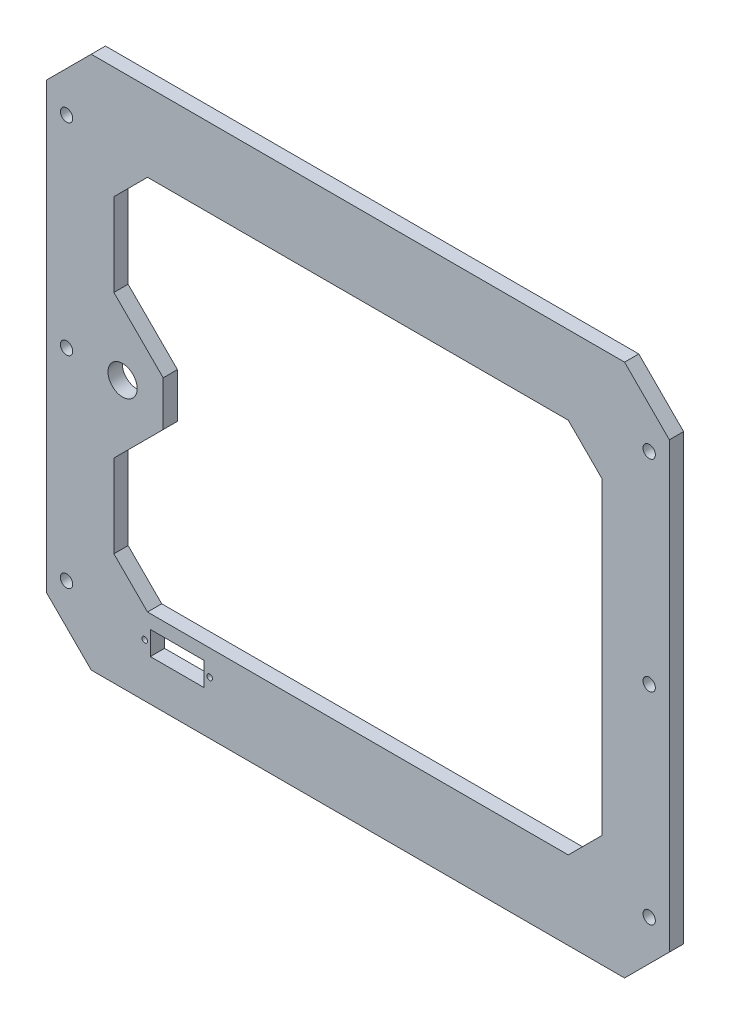
SolidWorks part; units mm, degrees
ref_plane "Front Plane" through (0, 0, 0) normal (0, 0, 1) x (1, 0, 0)
ref_plane "Top Plane" through (0, 0, 0) normal (0, 1, 0) x (1, 0, 0)
ref_plane "Right Plane" through (0, 0, 0) normal (1, 0, 0) x (0, 0, -1)
sketch "Sketch1" plane through (0, 0, 0) normal (0, 0, 1) x (1, 0, 0)
  line L0 (-79.0045, 0) -> (94.053, 0) construction
  line L1 (0, 67.0127) -> (0, -68.6587) construction
  line L3 (139, -119) -> (-139, -119)
  line L4 (139, -119) -> (139, 119)
  line L5 (139, 119) -> (-139, 119)
  line L6 (-139, -119) -> (-139, 119)
  line L7 (139, -119) -> (-139, 119) construction
  line L8 (139, 119) -> (-139, -119) construction
  point P4 (0, 0)
  dimension "D1" = 238
  dimension "D2" = 278
extrude "Boss-Extrude1" add sketch "Sketch1" along normal blind 6.35
chamfer "Chamfer1" distance 20 angle 45 4 edges at (139, -119, 3.175) (139, 119, 3.175) (-139, 119, 3.175) (-139, -119, 3.175)
sketch "Sketch4" plane through (0, 0, 6.35) normal (0, 0, 1) x (1, 0, 0)
  line L0 (0, 186.846) -> (0, -174.5938) construction
  line L1 (219.7737, 0) -> (-232.7917, 0) construction
  line L4 (-139, 99) -> (-139, -99) construction
  circle A6 centre (-130, 90) radius 2.75
  circle A7 centre (-130, -90) radius 2.75
  circle A8 centre (-130, 0) radius 2.75
  circle A9 centre (130, -90) radius 2.75
  circle A10 centre (130, 0) radius 2.75
  circle A11 centre (130, 90) radius 2.75
  dimension "D6" = 5.5
  dimension "D7" = 5.5
  dimension "D4" = 9
  dimension "D5" = 90
extrude "Cut-Extrude2" cut sketch "Sketch4" against normal blind 76.2
sketch "Sketch5" plane through (0, 0, 6.35) normal (0, 0, 1) x (1, 0, 0)
  line L0 (-139, 99) -> (-139, -99) construction
  line L1 (119, 119) -> (-119, 119) construction
  line L2 (93.8757, -84) -> (-93.8757, -84)
  line L3 (108.8757, -69) -> (108.8757, 69)
  line L4 (93.8757, 84) -> (-93.8757, 84)
  line L5 (-108.8757, -69) -> (-108.8757, -32)
  line L6 (108.8757, -84) -> (-108.8757, 84) construction
  line L7 (108.8757, 84) -> (-108.8757, -84) construction
  line L8 (-108.8757, 69) -> (-93.8757, 84)
  line L9 (108.8757, 69) -> (93.8757, 84)
  line L10 (93.8757, -84) -> (108.8757, -69)
  line L11 (-93.8757, -84) -> (-108.8757, -69)
  line L12 (-109, 0) -> (0, 0) construction
  line L13 (-108.8757, 32) -> (-86.8757, 10)
  line L14 (-86.8757, 10) -> (-86.8757, -10)
  line L15 (-108.8757, -32) -> (-86.8757, -10)
  line L16 (-108.8757, 32) -> (-108.8757, 69)
  circle A0 centre (-105, 0) radius 6.5
  point P4 (0, 0)
  point P26 (-86.8757, 0)
  point P27 (0, 0)
  dimension "D1" = 13
  dimension "D2" = 34
  dimension "D3" = 35
  dimension "D4" = 45
  dimension "D5" = 20
  dimension "D10" = 22
extrude "Cut-Extrude3" cut sketch "Sketch5" against normal blind 10
sketch "Sketch7" plane through (0, 0, 6.35) normal (0, 0, 1) x (1, 0, 0)
  line L0 (-80.6158, -78.493) -> (-80.6158, -110.3099) construction
  line L1 (-92.6158, -90.0921) -> (-68.6158, -90.0921)
  line L2 (-92.6158, -90.0921) -> (-92.6158, -100.5921)
  line L3 (-92.6158, -100.5921) -> (-68.6158, -100.5921)
  line L4 (-68.6158, -90.0921) -> (-68.6158, -100.5921)
  line L5 (-92.6158, -90.0921) -> (-68.6158, -100.5921) construction
  line L6 (-92.6158, -100.5921) -> (-68.6158, -90.0921) construction
  circle A0 centre (-66.1158, -95.3421) radius 1.25
  circle A1 centre (-95.1158, -95.3421) radius 1.25
  point P0 (-80.6158, -95.3421)
  dimension "D2" = 2.5
  dimension "D1" = 29
extrude "Cut-Extrude4" cut sketch "Sketch7" against normal through all
equation "\"plate_thickness\"= 6.35 'thickness of the plate "
equation "\"D1@Boss-Extrude1\"=\"plate_thickness\""
equation "\"connector_D1\"= 70 'the big holes diameter"
equation "\"mtg_hole_D\"= 5.5 'mounting holes"
equation "\"mtg_dfc\"= 40 'mounting hole distance from center"
equation "\"t_height\"= 200"
equation "\"t_width\"= 240"
equation "\"t_length\"= 240"
equation "\"plate_hole_from_edge\"= 9"
equation "\"plate_spacing\"= 1"
equation "\"front_plate_height\"= \"t_height\" + 38"
equation "\"front_plate_width\"= \"t_width\" + 38"
equation "\"side_plate_height\"= \"front_plate_height\""
equation "\"side_plate_length\"= \"t_length\" + 38"
equation "\"top_plate_width\"= \"front_plate_width\""
equation "\"top_plate_length\"= \"side_plate_length\""
equation "\"D2@Sketch1\"=\"side_plate_length\""
equation "\"D1@Sketch1\"=\"side_plate_height\""
equation "\"D4@Sketch4\"=\"plate_hole_from_edge\""
equation "\"D6@Sketch4\"=\"mtg_hole_D\""
equation "\"D7@Sketch4\"=\"mtg_hole_D\""
